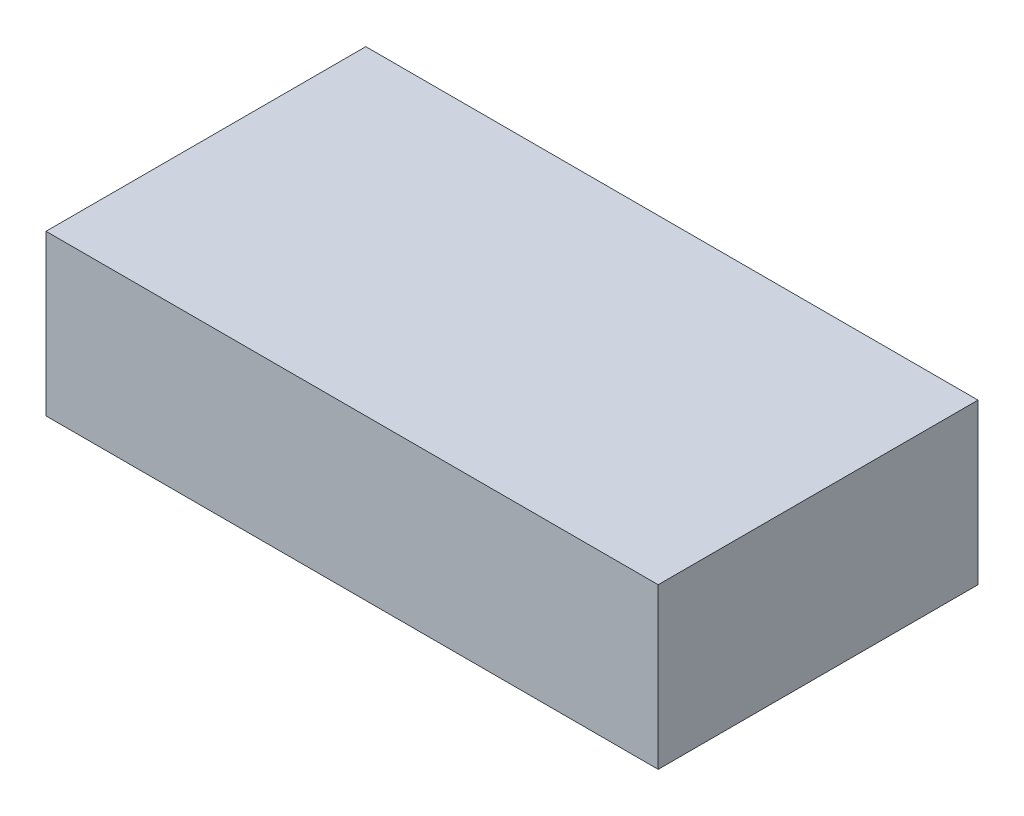
SolidWorks part; units mm, degrees
material "Custom Plastic"
ref_plane "Front Plane" through (0, 0, 0) normal (0, 0, 1) x (1, 0, 0)
ref_plane "Top Plane" through (0, 0, 0) normal (0, 1, 0) x (1, 0, 0)
ref_plane "Right Plane" through (0, 0, 0) normal (1, 0, 0) x (0, 0, -1)
sketch "Sketch1" plane through (0, 0, 0) normal (0, 1, 0) x (1, 0, 0)
  line L1 (-55.0593, 25.0395) -> (78.9407, 25.0395)
  line L2 (-55.0593, 25.0395) -> (-55.0593, -44.9605)
  line L3 (-55.0593, -44.9605) -> (78.9407, -44.9605)
  line L4 (78.9407, 25.0395) -> (78.9407, -44.9605)
  dimension "D1" = 70
  dimension "D2" = 134
extrude "Boss-Extrude1" add sketch "Sketch1" along normal blind 35
